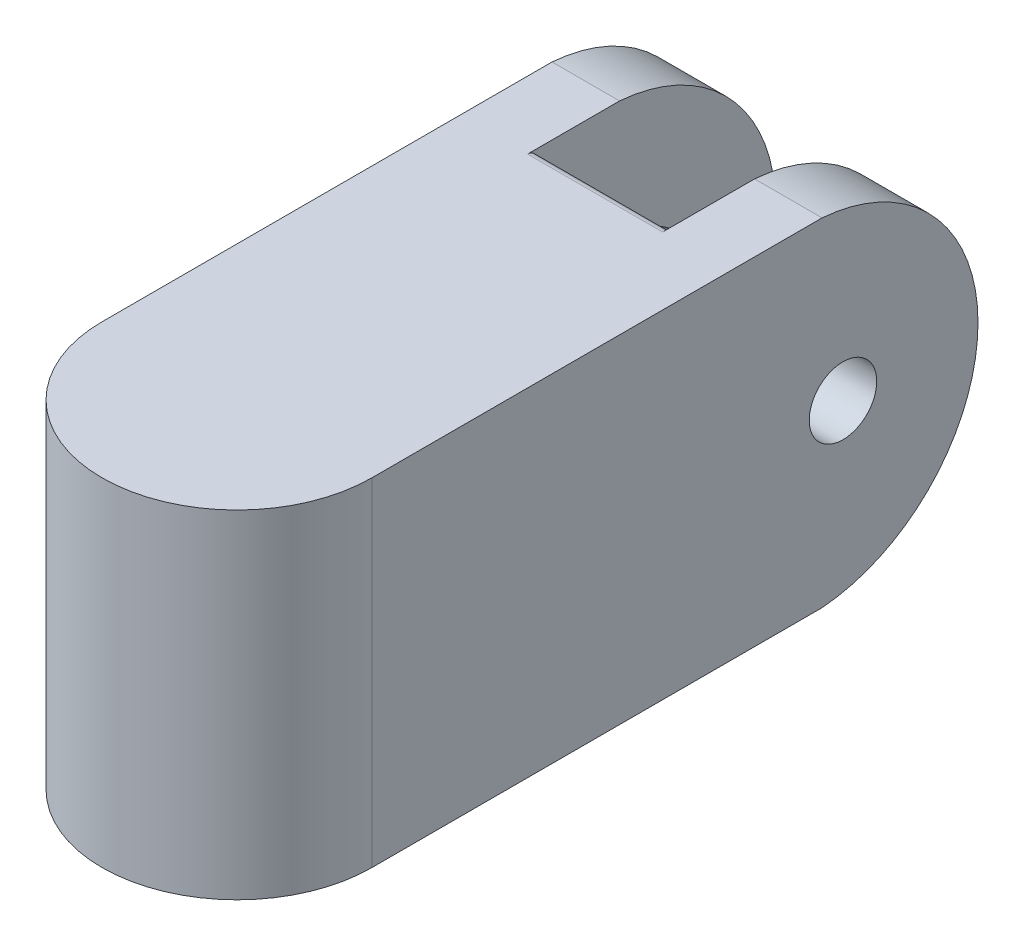
SolidWorks part; units mm, degrees
material "ABS PC"
ref_plane "Front Plane" through (0, 0, 0) normal (0, 0, 1) x (1, 0, 0)
ref_plane "Top Plane" through (0, 0, 0) normal (0, 1, 0) x (1, 0, 0)
ref_plane "Right Plane" through (0, 0, 0) normal (1, 0, 0) x (0, 0, -1)
sketch "Sketch1" plane through (0, 0, 0) normal (0, 0, 1) x (1, 0, 0)
  line L1 (-7.62, -9.525) -> (7.62, -9.525)
  line L2 (-7.62, -9.525) -> (-7.62, 9.525)
  line L3 (-7.62, 9.525) -> (7.62, 9.525)
  line L4 (7.62, -9.525) -> (7.62, 9.525)
  line L5 (-7.62, -9.525) -> (7.62, 9.525) construction
  line L6 (-7.62, 9.525) -> (7.62, -9.525) construction
  point P0 (0, 0)
  dimension "D1" = 15.24
  dimension "D2" = 19.05
extrude "Boss-Extrude1" add sketch "Sketch1" along normal blind 25.4
ref_plane "Plane2" through (7.62, 0, 0) normal (1, 0, 0) x (0, 0, -1)
sketch "Sketch9" plane through (7.62, 0, 0) normal (1, 0, 0) x (0, 0, -1)
  line L0 (0, 9.525) -> (0, -9.525)
  arc A0 (0, 9.525) -> (0, -9.525) centre (-0.7565, 0) cw
  dimension "D1" = 9.555
extrude "Boss-Extrude5" add sketch "Sketch9" against normal blind 3.81
pattern_linear "LPattern2" count 2 spacing 11.43 along (-1, 0, 0) of "Boss-Extrude5"
sketch "Sketch10" plane through (7.62, 0, 0) normal (1, 0, 0) x (0, 0, -1)
  line L0 (8.382, 0) -> (-8.382, 0) construction
  circle A0 centre (1.1785, 0) radius 1.905
  arc A1 (0, -9.525) -> (0, 9.525) centre (-0.7565, 0) ccw construction
  point P4 (8.7985, 0)
  dimension "D1" = 7.62
  dimension "D2" = 3.81
extrude "Cut-Extrude1" cut sketch "Sketch10" against normal through all contours A0
ref_plane "Plane5" through (0, -9.525, 0) normal (0, -1, 0) x (-1, 0, 0)
sketch "Sketch13" plane through (0, -9.525, 0) normal (0, -1, 0) x (-1, 0, 0)
  line L0 (7.62, -25.4) -> (-7.62, -25.4)
  arc A0 (7.62, -25.4) -> (-7.62, -25.4) centre (0, -25.4) cw
  dimension "D1" = 7.62
extrude "Boss-Extrude6" add sketch "Sketch13" against normal blind 19.05
sketch "Sketch17" plane through (0, 0, 0) normal (1, 0, 0) x (0, 0, -1)
  line L0 (0, 9.525) -> (0, -9.525)
  arc A0 (0, 9.525) -> (0, -9.525) centre (-0.7565, 0) ccw
  dimension "D1" = 9.555
extrude "Cut-Extrude2" cut sketch "Sketch17" against normal mid plane 7.62
sketch "Sketch18" plane through (0, -9.525, 0) normal (0, -1, 0) x (-1, 0, 0)
  line L0 (3.0449, -17.0071) -> (6.8549, -17.0071)
  line L1 (-3.048, -17.0071) -> (-6.858, -17.0071)
  line L2 (6.858, -15.2291) -> (1.778, -15.2291)
  line L3 (-6.858, -15.2291) -> (-1.778, -15.2291)
  line L4 (1.778, -15.2291) -> (1.778, -1.5131)
  line L5 (-1.778, -15.2291) -> (-1.778, -1.5131)
  line L6 (3.81, -1.5131) -> (-3.81, -1.5131) construction
  arc A0 (3.5901, -27.9324) -> (-3.7647, -27.8531) centre (-0.0687, -26.1634) cw
  arc A1 (5.3573, -27.7364) -> (-5.6142, -27.5357) centre (-0.1091, -26.5769) cw
  arc A2 (0, -19.7996) -> (-3.7647, -27.8531) centre (11.3234, -29.9995) ccw
  arc A3 (0, -19.7996) -> (3.5901, -27.9324) centre (-11.5408, -29.7529) cw
  arc A4 (5.3573, -27.7364) -> (3.0449, -17.0071) centre (-8.3681, -25.0806) ccw
  arc A5 (-5.6142, -27.5357) -> (-3.048, -17.0071) centre (8.1895, -25.3231) cw
  arc A6 (6.8549, -17.0071) -> (6.858, -15.2291) centre (7.3483, -16.1189) cw
  arc A7 (-6.858, -15.2291) -> (-6.858, -17.0071) centre (-7.0142, -16.1181) cw
  arc A8 (1.778, -1.5131) -> (-1.778, -1.5131) centre (0, -1.5131) cw
  arc A9 (-7.62, -25.4) -> (7.62, -25.4) centre (0, -25.4) ccw construction
  point P24 (1.778, -1.5131)
  point P25 (-1.778, -1.5131)
  point P26 (0, -33.02)
  dimension "D5" = 15.24
  dimension "D6" = 15.24
  dimension "D7" = 5.588
  dimension "D8" = 4.064
  dimension "D9" = 13.9799
  dimension "D10" = 13.9799
  dimension "D11" = 1.016
  dimension "D12" = 4.1315
  dimension "D19" = 1.778
  dimension "D28" = 6.444
  dimension "D31" = 0.9026
  dimension "D1" = 8.89
  dimension "D2" = 8.89
  dimension "D3" = 1.778
  dimension "D4" = 1.8765
  dimension "D13" = 3.81
  dimension "D14" = 3.81
  dimension "D15" = 5.08
  dimension "D16" = 5.08
  dimension "D17" = 13.716
  dimension "D18" = 13.716
  dimension "D20" = 4.1338
  dimension "D21" = 1.778
  dimension "D22" = 1.778
  dimension "D23" = 7.3548
  dimension "D24" = 10.9715
  dimension "D25" = 2.1832
  dimension "D26" = 2.032
  dimension "D27" = 19.7996
  dimension "D29" = 2.9299
  dimension "D30" = 3.2525
hole_wizard "CBORE for #6 Pan Head Machine Screw1" positions "Sketch21" profile "Sketch20" counterbore size "#6" standard "ANSI Inch" end condition through all
sketch "Sketch21" plane through (-7.62, 0, 0) normal (-1, 0, 0) x (0, 0, 1)
  point P0 (-1.1785, 0)
sketch "Sketch20" plane through (-7.62, 0, -1.1785) normal (0, 1, 0) x (0, 0, 1)
  line L0 (0, 0) -> (0, 15.24)
  line L1 (0, 15.24) -> (1.875, 15.24)
  line L3 (1.875, 15.24) -> (1.875, 2.032)
  line L4 (1.875, 2.032) -> (3.75, 2.032)
  line L5 (3.75, 2.032) -> (3.75, 0)
  line L7 (3.75, 0) -> (0, 0)
  line L11 (0, -6.35) -> (0, 107.95) construction
  dimension "Thru Hole Dia." = 3.75
  dimension "Thru Hole Depth" = 15.24
  dimension "C'Bore Dia." = 7.5
  dimension "C'Bore Depth" = 2.032
sketch "Sketch22" plane through (-5.588, 0, 0) normal (-1, 0, 0) x (0, 0, 1)
  circle A0 centre (-1.1785, 0) radius 2.5
  circle A1 centre (-1.1785, 0) radius 1.905 construction
  dimension "D1" = 5
extrude "Cut-Extrude3" cut sketch "Sketch22" against normal up to surface (1.778 mm away)
fillet "Fillet1" radius 0.5 2 edges at (0, -9.525, 1.5131) (0, 9.525, 1.5131)
fillet "Fillet2" radius 0.5 2 edges at (-7.62, 0, 2.5715) (-5.588, 0, 2.5715)
extrude "Cut-Extrude4" cut sketch "Sketch18" against normal blind 1.27 contours A5 L1 A7 L3 L5 A8 L4 L2 A6 L0 A4 A1
sketch "Sketch23" plane through (0, -9.525, 0) normal (0, -1, 0) x (1, 0, 0)
  line L0 (0, 19.0083) -> (-3.8467, 27.023)
  line L1 (0, 19.0083) -> (3.7733, 27.0578)
  arc A0 (-3.8467, 27.023) -> (3.7733, 27.0578) centre (-0.0302, 25.6263) cw
  dimension "D4" = 4.064
  dimension "D1" = 8.89
  dimension "D2" = 8.89
  dimension "D3" = 7.62
extrude "Cut-Extrude6" cut sketch "Sketch23" against normal blind 3.048
fillet "Fillet3" radius 0.5 1 edges at (0, -8.255, 5.5683)
sketch "Sketch26" plane through (0, -6.477, 0) normal (0, -1, 0) x (-1, 0, 0)
  arc A0 (2.3423, -26.2909) -> (-2.2297, -26.2909) centre (0.0563, -26.2909) cw
  arc A1 (2.3423, -26.2909) -> (-2.2297, -26.2909) centre (0.0563, -28.3069) ccw
  dimension "D1" = 2.286
  dimension "D2" = 3.048
  dimension "D3" = 2.286
  dimension "D4" = 2.286
  dimension "D5" = 26.2909
  dimension "D6" = 0.8926
extrude "Cut-Extrude7" cut sketch "Sketch26" against normal blind 1.27
sketch "Sketch27" plane through (0, -5.207, 0) normal (0, -1, 0) x (1, 0, 0)
  circle A0 centre (-0.0563, 26.2909) radius 1.397
  dimension "D1" = 2.794
extrude "Cut-Extrude8" cut sketch "Sketch27" against normal blind 1.27 contours A0
